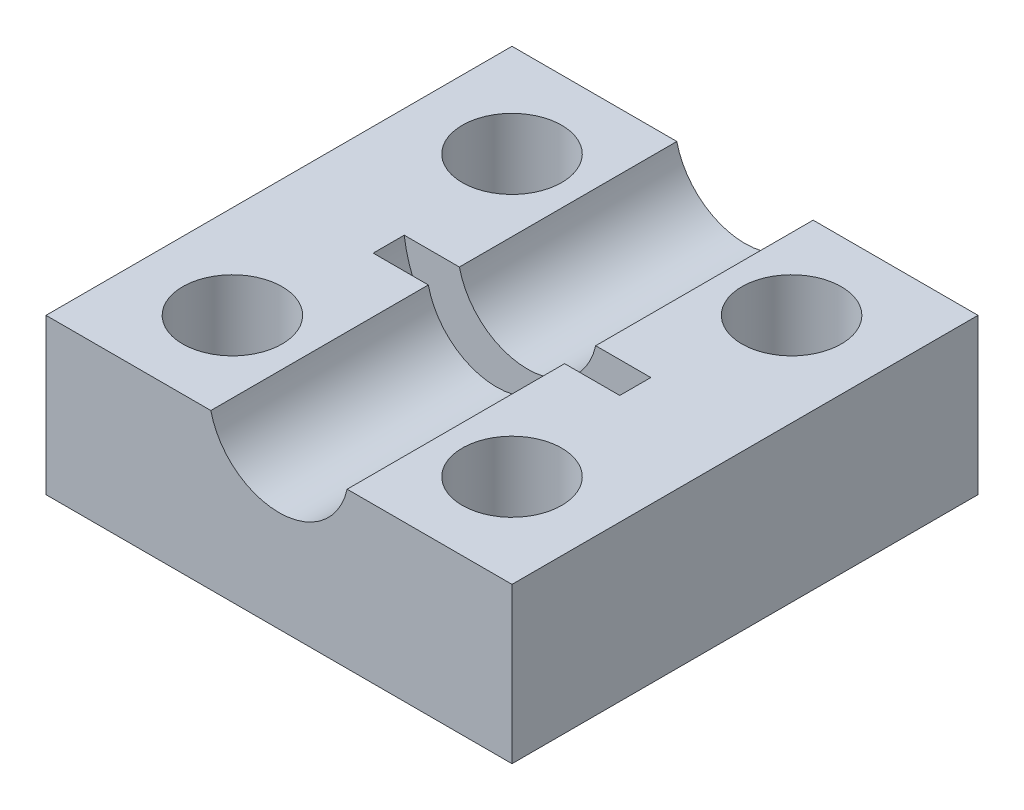
SolidWorks part; units mm, degrees
ref_plane "Ebene vorne" through (0, 0, 0) normal (0, 0, 1) x (1, 0, 0)
ref_plane "Ebene oben" through (0, 0, 0) normal (0, 1, 0) x (1, 0, 0)
ref_plane "Ebene rechts" through (0, 0, 0) normal (1, 0, 0) x (0, 0, -1)
sketch "Skizze1" plane through (0, 0, 0) normal (0, 1, 0) x (1, 0, 0)
  line L1 (-4.5, 4.5) -> (4.5, 4.5) construction
  line L2 (-4.5, 4.5) -> (-4.5, -4.5) construction
  line L3 (-4.5, -4.5) -> (4.5, -4.5) construction
  line L4 (4.5, 4.5) -> (4.5, -4.5) construction
  line L5 (-4.5, 4.5) -> (4.5, -4.5) construction
  line L6 (-4.5, -4.5) -> (4.5, 4.5) construction
  line L7 (-7.5, 7.5) -> (7.5, 7.5)
  line L8 (-7.5, 7.5) -> (-7.5, -7.5)
  line L9 (-7.5, -7.5) -> (7.5, -7.5)
  line L10 (7.5, 7.5) -> (7.5, -7.5)
  line L11 (-7.5, 7.5) -> (7.5, -7.5) construction
  line L12 (-7.5, -7.5) -> (7.5, 7.5) construction
  circle A0 centre (-4.5, 4.5) radius 1.6
  circle A1 centre (-4.5, -4.5) radius 1.6
  circle A2 centre (4.5, -4.5) radius 1.6
  circle A3 centre (4.5, 4.5) radius 1.6
  point P0 (0, 0)
  point P6 (0, 0)
  dimension "D5" = 3.2
  dimension "D1" = 9
  dimension "D2" = 9
  dimension "D3" = 15
  dimension "D4" = 15
extrude "Aufsatz-Linear austragen1" add sketch "Skizze1" along normal blind 5
sketch "Skizze2" plane through (0, 0, 7.5) normal (0, 0, 1) x (1, 0, 0)
  line L0 (-7.5, 5) -> (7.5, 5) construction
  circle A0 centre (0, 5.5) radius 2.25
  dimension "D2" = 4.5
  dimension "D1" = 0.5
extrude "Schnitt-Linear austragen1" cut sketch "Skizze2" against normal through all
ref_plane "Ebene1" through (0, 0, 0.5) normal (0, 0, 1) x (1, 0, 0)
sketch "Skizze3" plane through (0, 0, 0.5) normal (0, 0, 1) x (1, 0, 0)
  circle A0 centre (0, 5.5) radius 4
  dimension "D1" = 8
extrude "Schnitt-Linear austragen2" cut sketch "Skizze3" against normal blind 1
